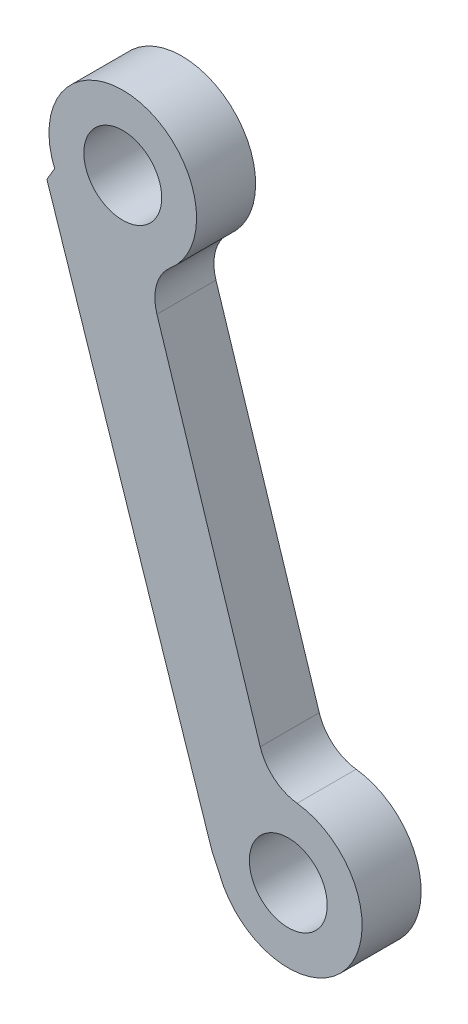
SolidWorks part; units mm, degrees
material "PLA"
ref_plane "Front Plane" through (0, 0, 0) normal (0, 0, 1) x (1, 0, 0)
ref_plane "Top Plane" through (0, 0, 0) normal (0, 1, 0) x (1, 0, 0)
ref_plane "Right Plane" through (0, 0, 0) normal (1, 0, 0) x (0, 0, -1)
ref_plane "Plane1" through (0, 0, 4) normal (0, 0, 1) x (1, 0, 0)
sketch "Sketch1" plane through (0, 0, 4) normal (0, 0, 1) x (1, 0, 0)
  line L0 (17.9521, 57.4484) -> (10.9551, 79.3317)
  line L1 (4.0228, 84.4074) -> (3.5003, 83.5205)
  line L2 (3.5003, 83.5205) -> (14.6727, 49.7283)
  line L3 (14.6727, 49.7283) -> (15.2001, 48.5968)
  line L4 (17.9521, 57.4484) -> (10.9614, 79.3118) construction
  line L5 (4.0228, 84.4074) -> (3.5003, 83.5205) construction
  circle A0 centre (19.8562, 50.419) radius 2.6375
  arc A1 (15.2001, 48.5968) -> (20.4521, 55.3834) centre (19.8562, 50.419) ccw
  arc A2 (20.4521, 55.3834) -> (17.9521, 57.4484) centre (20.8096, 58.362) cw
  arc A3 (10.9551, 79.3317) -> (11.8672, 82.5039) centre (13.7828, 80.2359) cw
  arc A4 (11.8672, 82.5039) -> (4.0228, 84.4074) centre (8.641, 86.3238) ccw
  circle A5 centre (8.641, 86.3238) radius 2.6375
  circle A6 centre (19.8562, 50.419) radius 2.6375 construction
  arc A7 (17.9521, 57.4484) -> (20.4521, 55.3834) centre (20.8096, 58.362) ccw construction
  arc A8 (11.8772, 82.5124) -> (4.0228, 84.4074) centre (8.641, 86.3238) ccw construction
  arc A9 (15.1167, 48.8262) -> (20.4521, 55.3834) centre (19.8562, 50.419) ccw construction
extrude "Boss-Extrude1" add sketch "Sketch1" against normal blind 4
